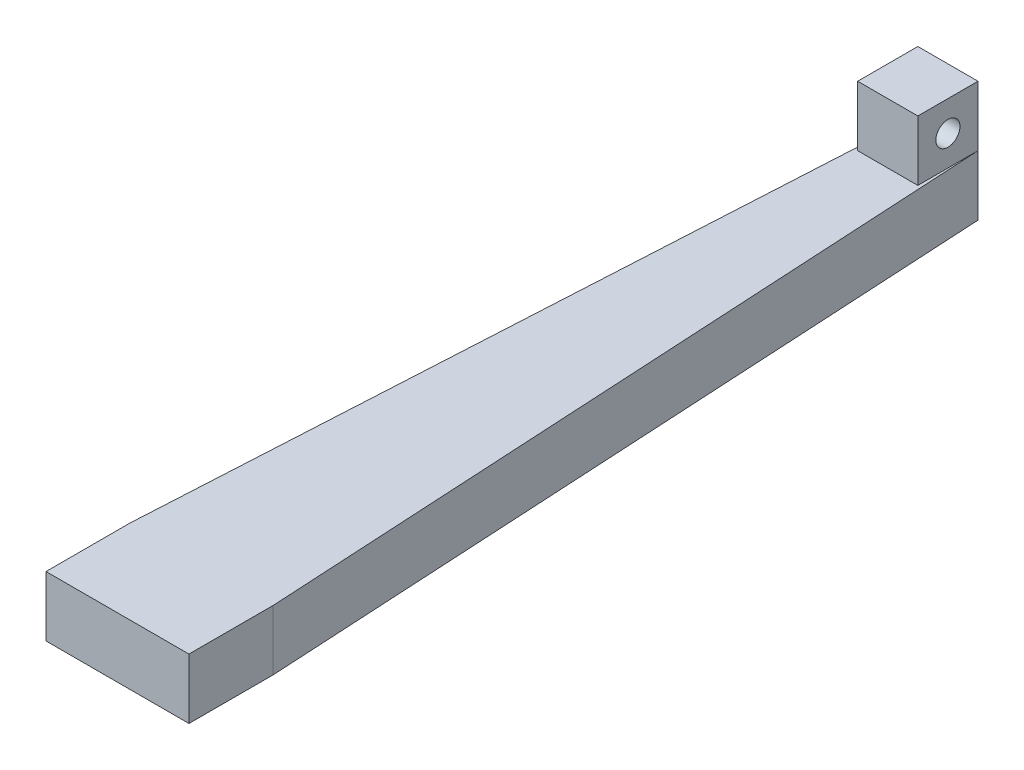
SolidWorks part; units mm, degrees
ref_plane "Front Plane" through (0, 0, 0) normal (0, 0, 1) x (1, 0, 0)
ref_plane "Top Plane" through (0, 0, 0) normal (0, 1, 0) x (1, 0, 0)
ref_plane "Right Plane" through (0, 0, 0) normal (1, 0, 0) x (0, 0, -1)
sketch "Sketch3" plane through (0, 0, 0) normal (0, 1, 0) x (1, 0, 0)
  line L1 (-110, 110) -> (110, 110)
  line L2 (-110, 110) -> (-110, -110)
  line L3 (-110, -110) -> (110, -110)
  line L4 (110, 110) -> (110, -110)
  line L5 (-110, 110) -> (110, -110) construction
  line L6 (-110, -110) -> (110, 110) construction
  point P0 (0, 0)
  dimension "D1" = 220
  dimension "D2" = 220
extrude "Boss-Extrude1" add sketch "Sketch3" along normal blind 10
sketch "Sketch4" plane through (0, 10, 0) normal (0, 1, 0) x (1, 0, 0)
  line L0 (-110, 110) -> (0, -110)
  line L1 (-110, -110) -> (110, -110) construction
  line L2 (0, -110) -> (110, 110)
  line L3 (110, 110) -> (110, -110)
  line L4 (110, -110) -> (0, -110)
  line L5 (0, -110) -> (-110, -110)
  line L6 (-110, -110) -> (-110, 110)
  line M1 (110, -110) -> (110, 110)
  line M3 (-110, 110) -> (-110, -110)
  line M4 (-110, -110) -> (110, -110)
extrude "Cut-Extrude1" cut sketch "Sketch4" against normal blind 10 contours L0 M3 M4 | L2 M4 M1
sketch "Sketch5" plane through (0, 0, 0) normal (0, -1, 0) x (1, 0, 0)
  line L6 (200, -200) -> (-200, -200)
  line L7 (200, -200) -> (200, 200)
  line L8 (200, 200) -> (-200, 200)
  line L9 (-200, -200) -> (-200, 200)
  line L10 (200, -200) -> (-200, 200) construction
  line L11 (200, 200) -> (-200, -200) construction
  line L12 (225, -225) -> (-225, -225)
  line L13 (225, -225) -> (225, 225)
  line L14 (225, 225) -> (-225, 225)
  line L15 (-225, -225) -> (-225, 225)
  point P0 (0, 0)
  point P5 (200, -225)
  point P6 (200, -200)
  point P8 (225, -225)
  point P9 (-225, 200)
  point P10 (-225, 225)
  dimension "D1" = 400
  dimension "D2" = 400
  dimension "D3" = 25
  dimension "D4" = 25
  dimension "D5" = 25
  dimension "D6" = 25
extrude "Boss-Extrude3" add sketch "Sketch5" against normal blind 25 separate body
sketch "Sketch8" plane through (0, 25, 0) normal (0, 1, 0) x (1, 0, 0)
  line L0 (-225, -225) -> (-225, 225) construction
  line L1 (225, 225) -> (225, -225) construction
  line L2 (-225, 200) -> (-200, 200)
  line L3 (-200, 200) -> (225, 200)
  line L4 (225, 200) -> (225, 225)
  line L5 (225, 225) -> (-225, 225)
  line L6 (-225, 225) -> (-225, 200)
  point P0 (-225, 200)
  point P1 (-200, 200)
  point P4 (200, 200)
  point P7 (225, 200)
extrude "Cut-Extrude2" cut sketch "Sketch8" against normal blind 25
sketch "Sketch9" plane through (0, 25, 0) normal (0, 1, 0) x (1, 0, 0)
  line L0 (-200, -200) -> (-200, 200) construction
  line L1 (-225, -225) -> (-225, 200) construction
  line L2 (225, 200) -> (225, -225) construction
  line L3 (-225, 150) -> (225, 150)
  line L4 (225, 150) -> (225, 200)
  line L5 (225, 200) -> (-225, 200)
  line L6 (-225, 200) -> (-225, 150)
  point P0 (-110, 110)
  point P1 (-200, 200)
  point P3 (-110, 150)
  point P5 (-200, 150)
  point P6 (-225, 150)
  point P9 (225, 150)
  dimension "D1" = 40
extrude "Cut-Extrude3" cut sketch "Sketch9" against normal blind 25
sketch "Sketch10" plane through (0, 25, 0) normal (0, 1, 0) x (1, 0, 0)
  line L0 (-200, -200) -> (-200, 150) construction
  line L1 (-225, -225) -> (-225, 150) construction
  line L2 (225, 150) -> (225, -225) construction
  line L4 (-225, 110) -> (225, 110)
  line L5 (-225, 110) -> (-225, 150)
  line L6 (-225, 150) -> (225, 150)
  line L7 (225, 110) -> (225, 150)
  point P0 (-200, 110)
  point P1 (-225, 110)
  point P4 (225, 110)
extrude "Cut-Extrude4" cut sketch "Sketch10" against normal blind 25
sketch "Sketch11" plane through (0, 0, -110) normal (0, 0, -1) x (-1, 0, 0)
  line L1 (225, 0) -> (200, 0)
  line L2 (225, 0) -> (225, 25)
  line L3 (225, 25) -> (200, 25)
  line L4 (200, 0) -> (200, 25)
  line L5 (-200, 0) -> (-225, 0)
  line L6 (-200, 0) -> (-200, 25)
  line L7 (-200, 25) -> (-225, 25)
  line L8 (-225, 0) -> (-225, 25)
extrude "Boss-Extrude5" add sketch "Sketch11" along normal blind 25
sketch "Sketch12" plane through (-200, 0, 0) normal (1, 0, 0) x (0, 0, -1)
  line L0 (-200, 0) -> (135, 0) construction
  line L1 (135, 25) -> (110, 25)
  line L2 (135, 25) -> (135, 0)
  line L3 (135, 0) -> (110, 0)
  line L4 (110, 25) -> (110, 0)
  dimension "D1" = 25
extrude "Boss-Extrude6" add sketch "Sketch12" along normal blind 25
sketch "Sketch13" plane through (200, 0, 0) normal (-1, 0, 0) x (0, 0, 1)
  line L0 (-135, 25) -> (200, 25) construction
  line L1 (-135, 0) -> (-110, 0)
  line L2 (-135, 0) -> (-135, 25)
  line L3 (-135, 25) -> (-110, 25)
  line L4 (-110, 0) -> (-110, 25)
  dimension "D1" = 25
extrude "Boss-Extrude7" add sketch "Sketch13" along normal blind 25
sketch "Sketch14" plane through (0, 25, 0) normal (0, 1, 0) x (1, 0, 0)
  line L0 (-175, 110) -> (-200, 110) construction
  line L1 (175, 110) -> (200, 110) construction
  circle A0 centre (-187.5, 122.5) radius 5
  circle A1 centre (187.5, 122.5) radius 5
  point P0 (-187.5, 110)
  point P1 (-187.5, 122.5)
  point P6 (187.5, 110)
  point P7 (187.5, 122.5)
extrude "Cut-Extrude5" cut sketch "Sketch14" against normal blind 25
sketch "Sketch15" plane through (-225, 0, 0) normal (-1, 0, 0) x (0, 0, 1)
  line L0 (225, 0) -> (225, -20)
  line L1 (225, -20) -> (-135, 0)
  line L2 (-135, 0) -> (225, 0)
  line L3 (225, 25) -> (225, 45)
  line L4 (225, 45) -> (-135, 25)
  line L5 (-135, 25) -> (225, 25)
  point P0 (225, 0)
  point P1 (225, -20)
  point P3 (225, 45)
  point P7 (225, 25)
  dimension "D1" = 20
  dimension "D2" = 20
extrude "Boss-Extrude8" add sketch "Sketch15" against normal blind 25
sketch "Sketch16" plane through (225, 0, 0) normal (1, 0, 0) x (0, 0, -1)
  line L0 (-225, 45) -> (-225, 25)
  line L1 (-225, 25) -> (135, 25)
  line L2 (135, 25) -> (-225, 45)
  line L3 (-225, 0) -> (-225, -20)
  line L4 (-225, -20) -> (135, 0)
  line L5 (135, 0) -> (-225, 0)
  point P0 (-225, 45)
  point P1 (-225, -20)
  point P3 (-225, 25)
  point P5 (-225, 0)
  point P7 (135, 0)
  point P9 (135, 25)
extrude "Boss-Extrude9" add sketch "Sketch16" against normal blind 25
sketch "Sketch17" plane through (0, 10, 0) normal (0, 1, 0) x (1, 0, 0)
  line L0 (-110, 110) -> (110, 110)
  line L1 (110, 110) -> (0, -110)
  line L2 (0, -110) -> (-110, 110)
extrude "Cut-Extrude6" cut sketch "Sketch17" against normal blind 25
sketch "Sketch18" plane through (-225, 0, 0) normal (-1, 0, 0) x (0, 0, 1)
  line L0 (225, -20) -> (225, 45)
  line L1 (225, 45) -> (225, 125)
  line L2 (225, 45) -> (-135, 25) construction
  line L3 (175.077, 42.2265) -> (225, 125)
  line L4 (175.077, 42.2265) -> (225, 45)
  line L5 (-135, 0) -> (225, -20) construction
  line L6 (225, -100) -> (225, -20)
  line L7 (175.077, -17.2265) -> (225, -100)
  line L8 (225, -20) -> (175.077, -17.2265)
  point P0 (225, 45)
  point P5 (175.077, 42.2265)
  point P10 (225, -100)
  point P11 (175.077, -17.2265)
  line M3 (225, 45) -> (-135, 25)
  line M5 (-135, 0) -> (225, -20)
  dimension "D1" = 80
  dimension "D2" = 50
  dimension "D3" = 80
extrude "Boss-Extrude10" add sketch "Sketch18" against normal blind 25 contours L3 L1 M3 | L7 L6 M5
sketch "Sketch19" plane through (225, 0, 0) normal (1, 0, 0) x (0, 0, -1)
  line L0 (-225, 125) -> (-225, 45)
  line L1 (-225, 45) -> (-175.077, 42.2265)
  line L2 (-175.077, 42.2265) -> (-225, 125)
  line L3 (-225, -20) -> (-225, -100)
  line L4 (-225, -100) -> (-175.077, -17.2265)
  line L5 (-175.077, -17.2265) -> (-225, -20)
  point P0 (-225, 45)
  point P1 (-225, 125)
  point P3 (-175.077, 42.2265)
  point P5 (-175.077, -17.2265)
  point P7 (-225, -20)
  point P9 (-225, -100)
extrude "Boss-Extrude11" add sketch "Sketch19" against normal blind 25
sketch "Sketch20" plane through (-200, 0, 0) normal (1, 0, 0) x (0, 0, -1)
  line L0 (-200, 25) -> (-225, 125)
  line L1 (-225, 125) -> (-225, 25)
  line L2 (-225, 25) -> (-200, 25)
extrude "Boss-Extrude12" add sketch "Sketch20" along normal blind 400
sketch "Sketch21" plane through (-200, 0, 0) normal (1, 0, 0) x (0, 0, -1)
  line L0 (-225, 0) -> (-225, -100)
  line L1 (-225, -100) -> (-200, 0)
  line L2 (-200, 0) -> (-225, 0)
extrude "Boss-Extrude13" add sketch "Sketch21" along normal blind 400
sketch "Sketch22" plane through (-225, 0, 0) normal (-1, 0, 0) x (0, 0, 1)
  line L0 (175.077, -17.2265) -> (175.077, 42.2265)
  line L1 (175.077, 42.2265) -> (225, 125)
  line L2 (225, 125) -> (225, -100)
  line L3 (225, -100) -> (175.077, -17.2265)
  point P0 (175.077, -17.2265)
  point P1 (175.077, 42.2265)
extrude "Cut-Extrude7" cut sketch "Sketch22" against normal blind 450
sketch "Sketch24" plane through (0, 0, 175.077) normal (0, 0, 1) x (1, 0, 0)
  line L1 (-225, 42.2265) -> (-175, 42.2265)
  line L2 (-225, 42.2265) -> (-225, -17.2265)
  line L3 (-225, -17.2265) -> (-175, -17.2265)
  line L4 (-175, 42.2265) -> (-175, -17.2265)
  point P0 (-175, 0)
  point P1 (-200, -17.2265)
  point P3 (-175, -17.2265)
extrude "Cut-Extrude8" cut sketch "Sketch24" against normal blind 350
sketch "Sketch25" plane through (0, 0, 175.077) normal (0, 0, 1) x (1, 0, 0)
  line L1 (200, 42.2265) -> (225, 42.2265)
  line L2 (200, 42.2265) -> (200, -17.2265)
  line L3 (200, -17.2265) -> (225, -17.2265)
  line L4 (225, 42.2265) -> (225, -17.2265)
extrude "Boss-Extrude14" add sketch "Sketch25" along normal blind 35
sketch "Sketch26" plane through (0, -17.2265, 0) normal (0, -1, 0) x (1, 0, 0)
  line L0 (-6.25, 86.275) -> (-14.85, 86.275)
  line L1 (-6.25, -86.275) -> (6.25, -86.275)
  line L2 (-6.25, -86.275) -> (-6.25, 86.275)
  line L3 (-6.25, 86.275) -> (6.25, 86.275)
  line L4 (6.25, -86.275) -> (6.25, 86.275)
  line L5 (-6.25, -86.275) -> (6.25, 86.275) construction
  line L6 (-6.25, 86.275) -> (6.25, -86.275) construction
  line L7 (-14.85, 86.275) -> (14.85, 86.275)
  line L8 (14.85, 86.275) -> (14.85, 68.775)
  line L9 (14.85, 68.775) -> (6.25, -86.275)
  line L10 (-6.25, -86.275) -> (-14.85, 68.775)
  line L11 (-14.85, 68.775) -> (-14.85, 86.275)
  point P0 (0, 0)
  point P6 (-14.85, 86.275)
  point P7 (14.85, 86.275)
  point P8 (-14.85, 68.775)
  point P10 (14.85, 68.775)
  dimension "D1" = 172.55
  dimension "D2" = 12.5
  dimension "D3" = 8.6
  dimension "D4" = 8.6
  dimension "D5" = 17.5
extrude "Boss-Extrude15" add sketch "Sketch26" against normal blind 12.5 separate body contours L1 L4 L3 L2 | L9 L8 L7 L4 | L11 L10 L2 L0
sketch "Sketch27" plane through (0, -4.7265, 0) normal (0, 1, 0) x (1, 0, 0)
  line L1 (-6.25, 86.275) -> (6.25, 86.275)
  line L2 (-6.25, 86.275) -> (-6.25, 73.775)
  line L3 (-6.25, 73.775) -> (6.25, 73.775)
  line L4 (6.25, 86.275) -> (6.25, 73.775)
  dimension "D1" = 12.5
extrude "Boss-Extrude16" add sketch "Sketch27" along normal blind 12.5
sketch "Sketch28" plane through (-6.25, 0, 0) normal (-1, 0, 0) x (0, 0, 1)
  line L0 (-86.275, 7.7735) -> (-73.775, 7.7735) construction
  line L1 (-86.275, 7.7735) -> (-86.275, -4.7265) construction
  circle A0 centre (-80.025, 1.5235) radius 2.5
  point P0 (-80.025, 7.7735)
  point P1 (-86.275, 1.5235)
  point P4 (-80.025, 1.5235)
extrude "Cut-Extrude9" cut sketch "Sketch28" against normal blind 12.5
sketch "Sketch29" plane through (0, 0, 210.077) normal (0, 0, 1) x (1, 0, 0)
  line L1 (153.2549, 71.1364) -> (269.4387, 71.1364)
  line L2 (153.2549, 71.1364) -> (153.2549, -48.9794)
  line L3 (153.2549, -48.9794) -> (269.4387, -48.9794)
  line L4 (269.4387, 71.1364) -> (269.4387, -48.9794)
  line L5 (153.2549, 71.1364) -> (269.4387, -48.9794) construction
  line L6 (153.2549, -48.9794) -> (269.4387, 71.1364) construction
  point P0 (211.3468, 11.0785)
extrude "Cut-Extrude10" cut sketch "Sketch29" against normal blind 800
